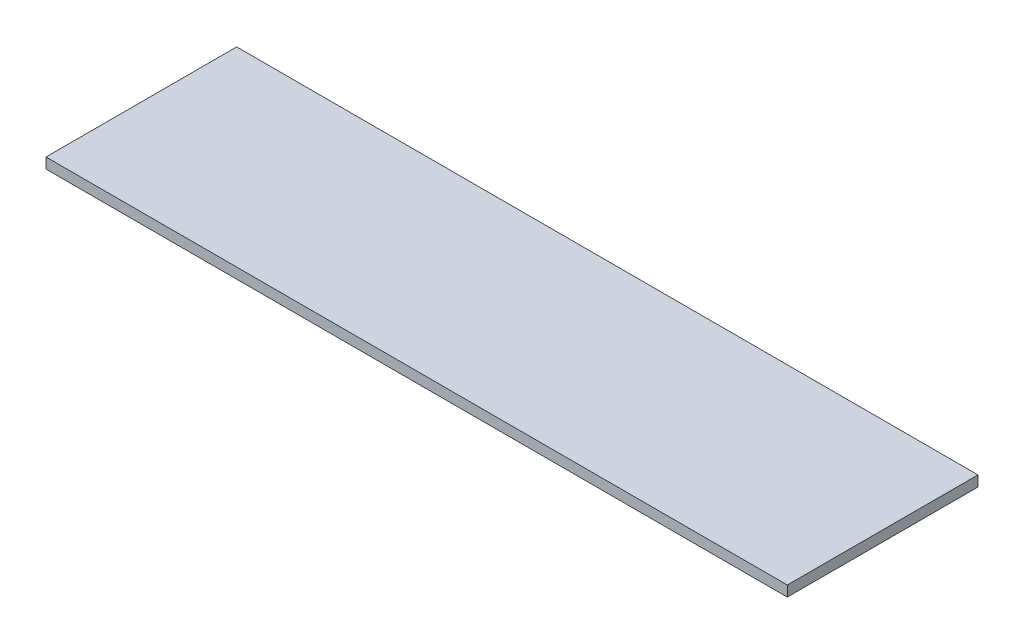
SolidWorks part; units mm, degrees
ref_plane "Plan de face" through (0, 0, 0) normal (0, 0, 1) x (1, 0, 0)
ref_plane "Plan de dessus" through (0, 0, 0) normal (0, 1, 0) x (1, 0, 0)
ref_plane "Plan de droite" through (0, 0, 0) normal (1, 0, 0) x (0, 0, -1)
sketch "Esquisse1" plane through (0, 0, 0) normal (0, 1, 0) x (1, 0, 0)
  line L0 (0, 0) -> (141.1613, 0)
  line L1 (141.1613, 0) -> (141.1613, 36.3076)
  line L2 (141.1613, 36.3076) -> (0, 36.3076)
  line L3 (0, 36.3076) -> (0, 0)
  point P4 (0, 0)
extrude "Boss.-Extru.1" add sketch "Esquisse1" along normal blind 2
